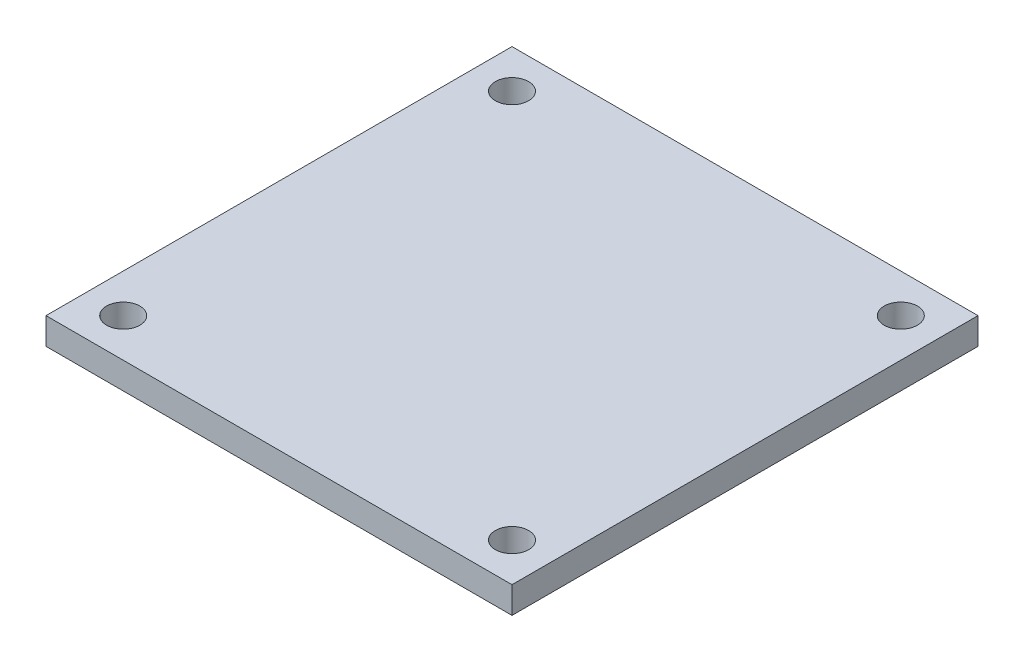
SolidWorks part; units mm, degrees
ref_plane "Front Plane" through (0, 0, 0) normal (0, 0, 1) x (1, 0, 0)
ref_plane "Top Plane" through (0, 0, 0) normal (0, 1, 0) x (1, 0, 0)
ref_plane "Right Plane" through (0, 0, 0) normal (1, 0, 0) x (0, 0, -1)
sketch "Sketch1" plane through (0, 0, 0) normal (0, 1, 0) x (1, 0, 0)
  line L1 (17.5, 17.5) -> (-17.5, 17.5)
  line L2 (17.5, 17.5) -> (17.5, -17.5)
  line L3 (17.5, -17.5) -> (-17.5, -17.5)
  line L4 (-17.5, 17.5) -> (-17.5, -17.5)
  line L5 (17.5, 17.5) -> (-17.5, -17.5) construction
  line L6 (17.5, -17.5) -> (-17.5, 17.5) construction
  point P0 (0, 0)
  dimension "D1" = 35
  dimension "D2" = 35
extrude "Boss-Extrude1" add sketch "Sketch1" along normal blind 2
sketch "Sketch2" plane through (0, 2, 0) normal (0, 1, 0) x (1, 0, 0)
  line L0 (0, -17.5) -> (0, 17.5)
  line L1 (-17.5, -17.5) -> (17.5, -17.5) construction
  line L2 (17.5, 17.5) -> (-17.5, 17.5) construction
  line L3 (17.5, 0) -> (-17.5, 0)
  line L4 (17.5, -17.5) -> (17.5, 17.5) construction
  line L5 (-17.5, 17.5) -> (-17.5, -17.5) construction
  circle A0 centre (-14.6, -14.6) radius 1.25
  circle A1 centre (14.6, -14.6) radius 1.25
  circle A2 centre (-14.6, 14.6) radius 1.25
  circle A3 centre (14.6, 14.6) radius 1.25
  dimension "D1" = 32.1
  dimension "D2" = 32.1
extrude "Cut-Extrude1" cut sketch "Sketch2" against normal through all contours A1 | A0 | A2 | A3
